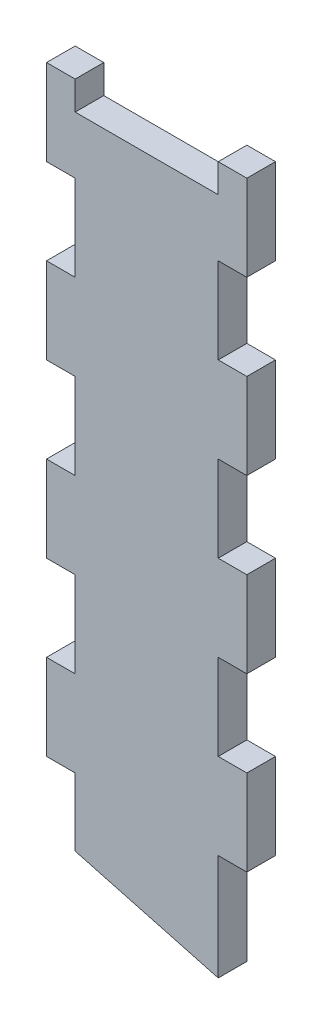
SolidWorks part; units mm, degrees
ref_plane "Front Plane" through (0, 0, 0) normal (0, 0, 1) x (1, 0, 0)
ref_plane "Top Plane" through (0, 0, 0) normal (0, 1, 0) x (1, 0, 0)
ref_plane "Right Plane" through (0, 0, 0) normal (1, 0, 0) x (0, 0, -1)
sketch "Model" plane through (0, 0, 0) normal (0, 0, 1) x (1, 0, 0)
  line L0 (22.6408, 12.9867) -> (52.6408, 4.9482)
  line L1 (22.6408, 153.1791) -> (16.6408, 153.1791)
  line L2 (16.6408, 153.1791) -> (16.6408, 135.1791)
  line L3 (16.6408, 135.1791) -> (22.6408, 135.1791)
  line L4 (22.6408, 117.1791) -> (16.6408, 117.1791)
  line L5 (16.6408, 117.1791) -> (16.6408, 99.1791)
  line L6 (16.6408, 99.1791) -> (22.6408, 99.1791)
  line L7 (22.6408, 81.1791) -> (16.6408, 81.1791)
  line L8 (16.6408, 81.1791) -> (16.6408, 63.1791)
  line L9 (16.6408, 63.1791) -> (22.6408, 63.1791)
  line L10 (22.6408, 45.1791) -> (16.6408, 45.1791)
  line L11 (16.6408, 45.1791) -> (16.6408, 27.1791)
  line L12 (16.6408, 27.1791) -> (22.6408, 27.1791)
  line L13 (52.6408, 153.1791) -> (58.6408, 153.1791)
  line L14 (58.6408, 153.1791) -> (58.6408, 135.1791)
  line L15 (58.6408, 135.1791) -> (52.6408, 135.1791)
  line L16 (52.6408, 117.1791) -> (58.6408, 117.1791)
  line L17 (58.6408, 117.1791) -> (58.6408, 99.1791)
  line L18 (58.6408, 99.1791) -> (52.6408, 99.1791)
  line L19 (52.6408, 81.1791) -> (58.6408, 81.1791)
  line L20 (58.6408, 81.1791) -> (58.6408, 63.1791)
  line L21 (58.6408, 63.1791) -> (52.6408, 63.1791)
  line L22 (52.6408, 45.1791) -> (58.6408, 45.1791)
  line L23 (58.6408, 45.1791) -> (58.6408, 27.1791)
  line L24 (58.6408, 27.1791) -> (52.6408, 27.1791)
  line L25 (22.6408, 135.1791) -> (22.6408, 117.1791)
  line L26 (22.6408, 99.1791) -> (22.6408, 81.1791)
  line L27 (22.6408, 63.1791) -> (22.6408, 45.1791)
  line L28 (22.6408, 27.1791) -> (22.6408, 12.9867)
  line L29 (52.6408, 4.9482) -> (52.6408, 27.1791)
  line L30 (52.6408, 45.1791) -> (52.6408, 63.1791)
  line L31 (52.6408, 81.1791) -> (52.6408, 99.1791)
  line L32 (52.6408, 117.1791) -> (52.6408, 135.1791)
  line L33 (22.6408, 153.1791) -> (22.6408, 147.1791)
  line L34 (22.6408, 147.1791) -> (52.6408, 147.1791)
  line L35 (52.6408, 147.1791) -> (52.6408, 153.1791)
extrude "Boss-Extrude1" add sketch "Model" along normal blind 6 contours L26 L7 L8 L9 L27 L10 L11 L12 L28 L0 L29 L24 L23 L22 L30 L21 L20 L19 L31 L18 L17 L16 L32 L15 L14 L13 L35 L34 L33 L1 L2 L3 L25 L4 L5 L6
